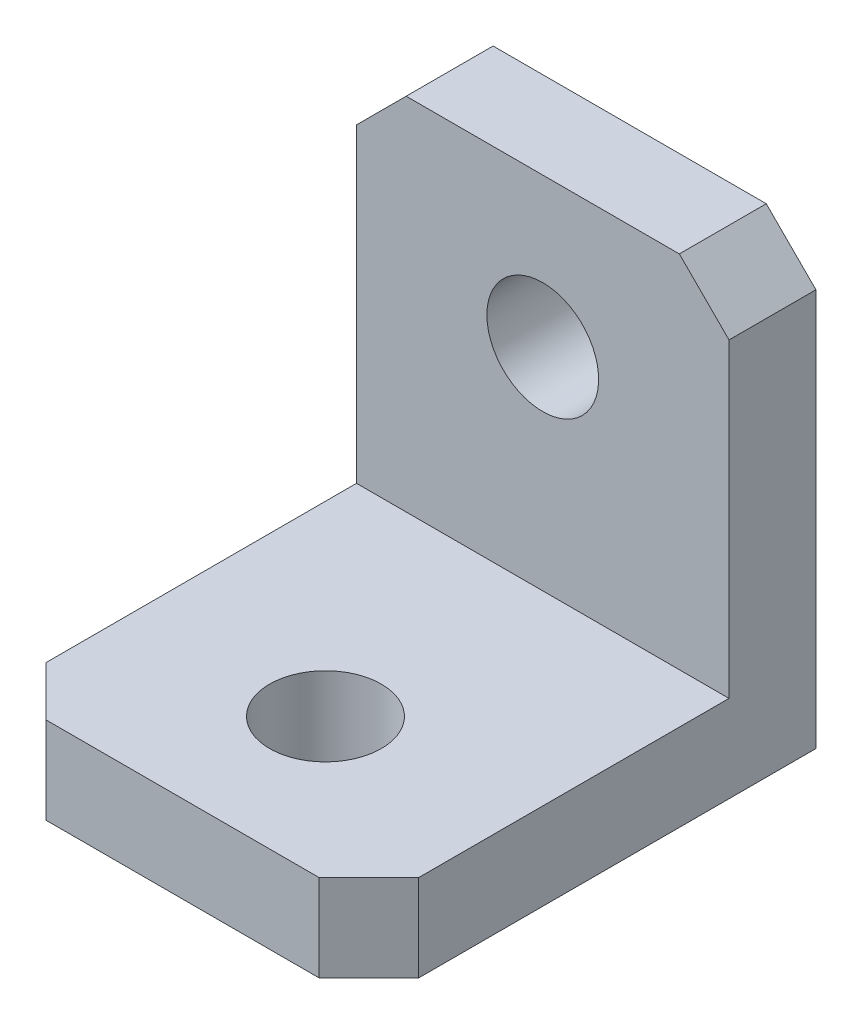
SolidWorks part; units mm, degrees
ref_plane "Alzado" through (0, 0, 0) normal (0, 0, 1) x (1, 0, 0)
ref_plane "Planta" through (0, 0, 0) normal (0, 1, 0) x (1, 0, 0)
ref_plane "Vista lateral" through (0, 0, 0) normal (1, 0, 0) x (0, 0, -1)
sketch "Croquis1" plane through (0, 0, 0) normal (1, 0, 0) x (0, 0, -1)
  line L0 (0, 0) -> (0, 3.5)
  line L1 (0, 3.5) -> (14.5, 3.5)
  line L2 (14.5, 3.5) -> (14.5, 18)
  line L3 (14.5, 18) -> (18, 18)
  line L4 (18, 18) -> (18, 0)
  line L5 (18, 0) -> (0, 0)
  dimension "D1" = 3.5
  dimension "D2" = 3.5
  dimension "D3" = 18
  dimension "D4" = 18
extrude "Saliente-Extruir1" add sketch "Croquis1" along normal mid plane 15
sketch "Croquis2" plane through (0, 0, 0) normal (0, -1, 0) x (1, 0, 0)
  line L0 (7.5, -18) -> (-7.5, -18) construction
  circle A0 centre (0, -5.75) radius 2.25
  point P4 (0, 0)
  dimension "D1" = 4.5
  dimension "D2" = 12.25
extrude "Cortar-Extruir1" cut sketch "Croquis2" against normal blind 15
sketch "Croquis3" plane through (0, 0, -18) normal (0, 0, -1) x (-1, 0, 0)
  line L0 (-7.5, 0) -> (7.5, 0) construction
  circle A0 centre (0, 12) radius 2.25
  point P2 (0, 0)
  dimension "D1" = 4.5
  dimension "D2" = 12
extrude "Cortar-Extruir2" cut sketch "Croquis3" against normal blind 15
chamfer "Chaflán1" distance 2 angle 45 4 edges at (7.5, 18, -16.25) (-7.5, 18, -16.25) (-7.5, 1.75, 0) (7.5, 1.75, 0)
